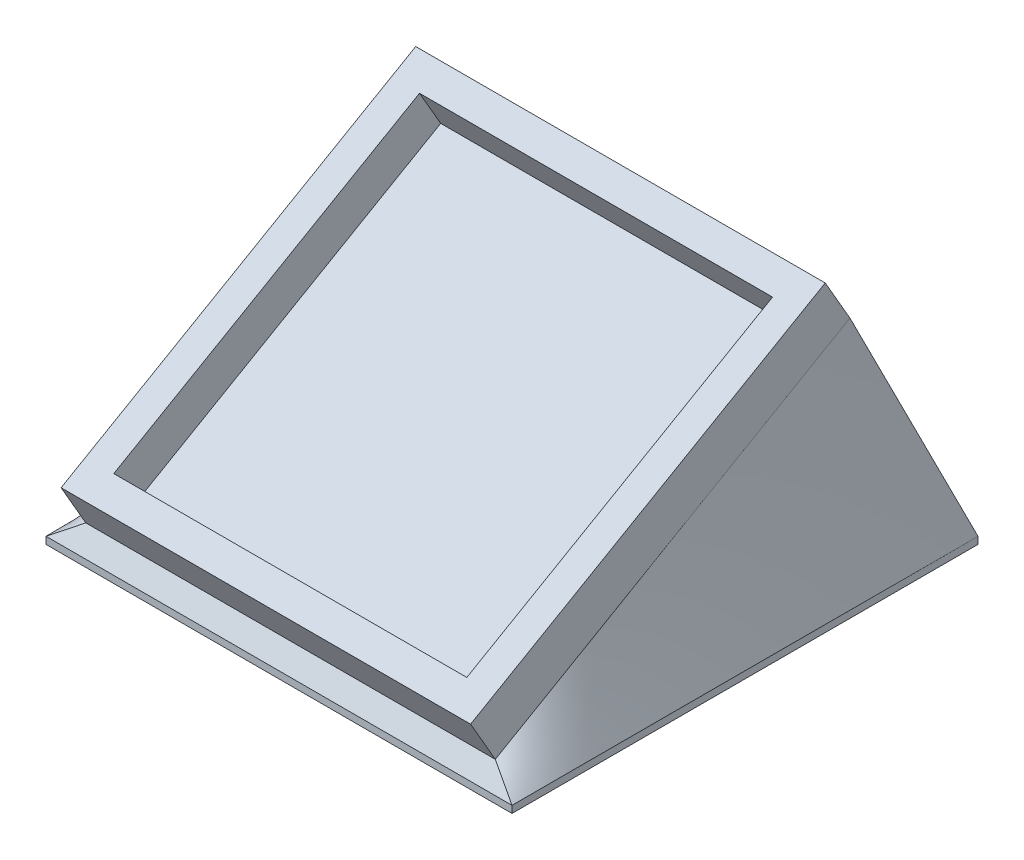
SolidWorks part; units mm, degrees
ref_plane "Front Plane" through (0, 0, 0) normal (0, 0, 1) x (1, 0, 0)
ref_plane "Top Plane" through (0, 0, 0) normal (0, 1, 0) x (1, 0, 0)
ref_plane "Right Plane" through (0, 0, 0) normal (1, 0, 0) x (0, 0, -1)
sketch "Sketch1" plane through (0, 0, 0) normal (0, 1, 0) x (1, 0, 0)
  line L1 (-22.2888, 13.0013) -> (14.5412, 13.0013)
  line L2 (-22.2888, 13.0013) -> (-22.2888, -23.8287)
  line L3 (-22.2888, -23.8287) -> (14.5412, -23.8287)
  line L4 (14.5412, 13.0013) -> (14.5412, -23.8287)
  dimension "D1" = 36.83
  dimension "D2" = 36.83
extrude "Boss-Extrude1" add sketch "Sketch1" along normal blind 0.635
sketch "Sketch2" plane through (0, 0.635, 0) normal (0, 1, 0) x (1, 0, 0)
  line L0 (14.5412, 13.0013) -> (-22.2888, 13.0013) construction
  line L1 (-19.7488, 10.4613) -> (12.0012, 10.4613)
  line L2 (-19.7488, 10.4613) -> (-19.7488, -21.2887)
  line L3 (-19.7488, -21.2887) -> (12.0012, -21.2887)
  line L4 (12.0012, 10.4613) -> (12.0012, -21.2887)
  line L5 (-22.2888, 13.0013) -> (-22.2888, -23.8287) construction
  line L7 (-22.2888, 13.0013) -> (14.5412, 13.0013)
  line L8 (-22.2888, 13.0013) -> (-22.2888, -23.8287)
  line L9 (-22.2888, -23.8287) -> (14.5412, -23.8287)
  line L10 (14.5412, 13.0013) -> (14.5412, -23.8287)
  dimension "D1" = 31.75
  dimension "D2" = 31.75
  dimension "D3" = 2.54
  dimension "D4" = 2.54
extrude "Boss-Extrude2" add sketch "Sketch2" along normal blind 3.81 contours L8 L7 L10 L9 | L2 L1 L4 L3
move or copy body "Body-Move/Copy1" bodies to move or copy 102 copy no translate (0, 12.7, 0)
sketch "Sketch3" plane through (0, 0, 0) normal (0, 1, 0) x (1, 0, 0)
  line L0 (-22.2888, 13.0013) -> (-22.2888, -23.8287) construction
  line L1 (-24.8288, 15.5413) -> (17.0812, 15.5413)
  line L2 (-24.8288, 15.5413) -> (-24.8288, -26.3687)
  line L3 (-24.8288, -26.3687) -> (17.0812, -26.3687)
  line L4 (17.0812, 15.5413) -> (17.0812, -26.3687)
  line L5 (-22.2888, -23.8287) -> (14.5412, -23.8287) construction
  dimension "D1" = 41.91
  dimension "D2" = 41.91
  dimension "D3" = 2.54
  dimension "D4" = 2.54
extrude "Boss-Extrude3" add sketch "Sketch3" along normal blind 0.635 separate body
move or copy body "Body-Move/Copy2" bodies to move or copy 103 copy no rotation origin (0, 4.7625, 5.4137) rotation axis (1, 0, 0) rotation angle 30
loft "Loft1" add section face at (-3.8738, 11.6366, 9.3825) section face at (-3.8738, 0.635, 5.4137)
sketch "Sketch4" plane through (0, 8.0539, -13.9498) normal (0, 0.5, -0.866) x (1, 0, 0)
  text T0 "30 x 0"
extrude "Cut-Extrude1" cut sketch "Sketch4" against normal blind 0.635
